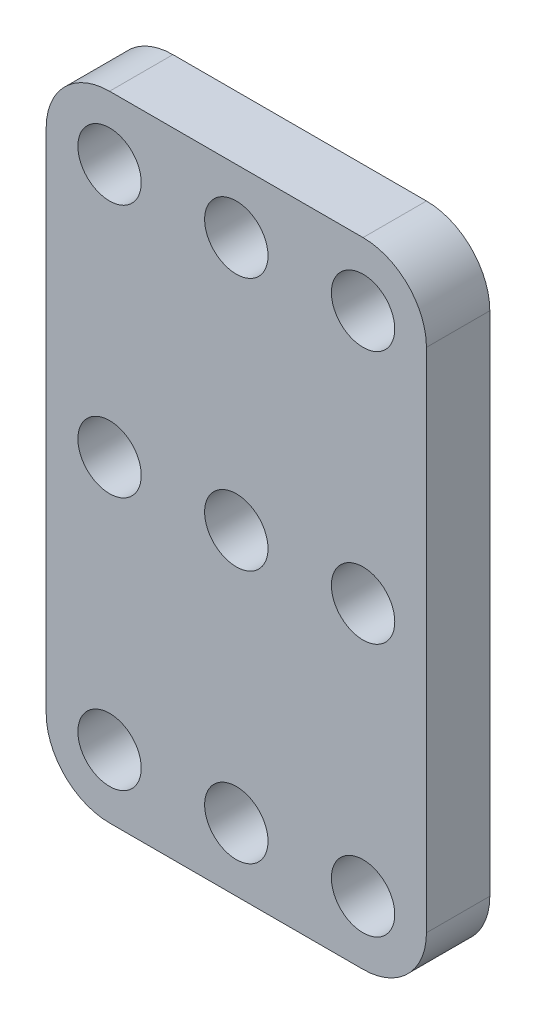
SolidWorks part; units mm, degrees
ref_plane "Front Plane" through (0, 0, 0) normal (0, 0, 1) x (1, 0, 0)
ref_plane "Top Plane" through (0, 0, 0) normal (0, 1, 0) x (1, 0, 0)
ref_plane "Right Plane" through (0, 0, 0) normal (1, 0, 0) x (0, 0, -1)
sketch "Çizim1" plane through (0, 0, 0) normal (0, 0, 1) x (1, 0, 0)
  line L1 (-64.0963, 22.8333) -> (-34.0963, 22.8333)
  line L2 (-64.0963, 22.8333) -> (-64.0963, -27.1667)
  line L3 (-64.0963, -27.1667) -> (-34.0963, -27.1667)
  line L4 (-34.0963, 22.8333) -> (-34.0963, -27.1667)
  circle A0 centre (-59.0963, 17.8333) radius 2.5
  circle A1 centre (-49.0963, 17.8333) radius 2.5
  circle A2 centre (-39.0963, 17.8333) radius 2.5
  circle A3 centre (-49.0963, -2.1667) radius 2.5
  circle A4 centre (-39.0963, -2.1667) radius 2.5
  circle A5 centre (-49.0963, -22.1667) radius 2.5
  circle A6 centre (-39.0963, -22.1667) radius 2.5
  circle A7 centre (-59.0963, -2.1667) radius 2.5
  circle A8 centre (-59.0963, -22.1667) radius 2.5
  dimension "D3" = 5
  dimension "D4" = 5
  dimension "D5" = 5
  dimension "D1" = 30
  dimension "D2" = 50
  dimension "D6" = 3
  dimension "D7" = 3
extrude "Boss-Extrude1" add sketch "Çizim1" along normal blind 5
fillet "Fillet1" radius 5 4 edges at (-64.0963, 22.8333, 2.5) (-64.0963, -27.1667, 2.5) (-34.0963, 22.8333, 2.5) (-34.0963, -27.1667, 2.5)
